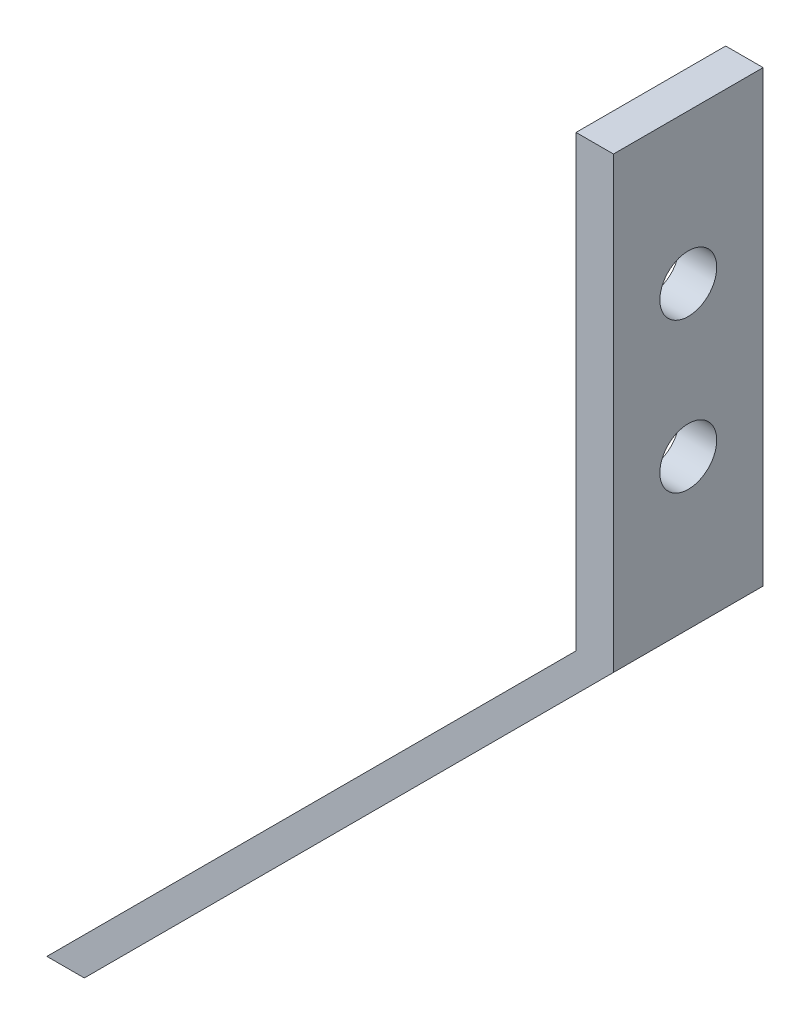
SolidWorks part; units mm, degrees
ref_plane "Front Plane" through (0, 0, 0) normal (0, 0, 1) x (1, 0, 0)
ref_plane "Top Plane" through (0, 0, 0) normal (0, 1, 0) x (1, 0, 0)
ref_plane "Right Plane" through (0, 0, 0) normal (1, 0, 0) x (0, 0, -1)
sketch "Sketch1" plane through (0, 0, 0) normal (0, 0, 1) x (1, 0, 0)
  line L0 (-3.175, 0) -> (-92.9776, -89.8026)
  line L1 (-3.175, 0) -> (3.175, 0)
  line L2 (-3.175, 0) -> (-3.175, 76.2)
  line L3 (-3.175, 76.2) -> (3.175, 76.2)
  line L4 (3.175, 0) -> (3.175, 76.2)
  line L5 (-92.9776, -89.8026) -> (-86.6276, -89.8026)
  line L6 (-86.6276, -89.8026) -> (3.175, 0)
  line L7 (3.175, 0) -> (-3.175, 0)
  dimension "D1" = 76.2
  dimension "D2" = 6.35
  dimension "D3" = 135
  dimension "D4" = 135
  dimension "D5" = 127
  dimension "D6" = 127
extrude "Boss-Extrude1" add sketch "Sketch1" along normal blind 25.4 contours L1 L4 L3 L2 | L5 L6 L1 L0
sketch "Sketch2" plane through (-3.175, 0, 0) normal (-1, 0, 0) x (0, 0, 1)
  line L0 (25.4, 76.2) -> (0, 76.2) construction
  line L1 (0, 0) -> (0, 76.2) construction
  circle A0 centre (12.7, 50.8) radius 4.826
  circle A1 centre (12.7, 25.4) radius 4.826
  point P8 (0, 0)
  dimension "D1" = 9.652
  dimension "D2" = 9.652
  dimension "D3" = 25.4
  dimension "D4" = 25.4
  dimension "D5" = 12.7
  dimension "D6" = 12.7
extrude "Cut-Extrude1" cut sketch "Sketch2" against normal blind 25.4
